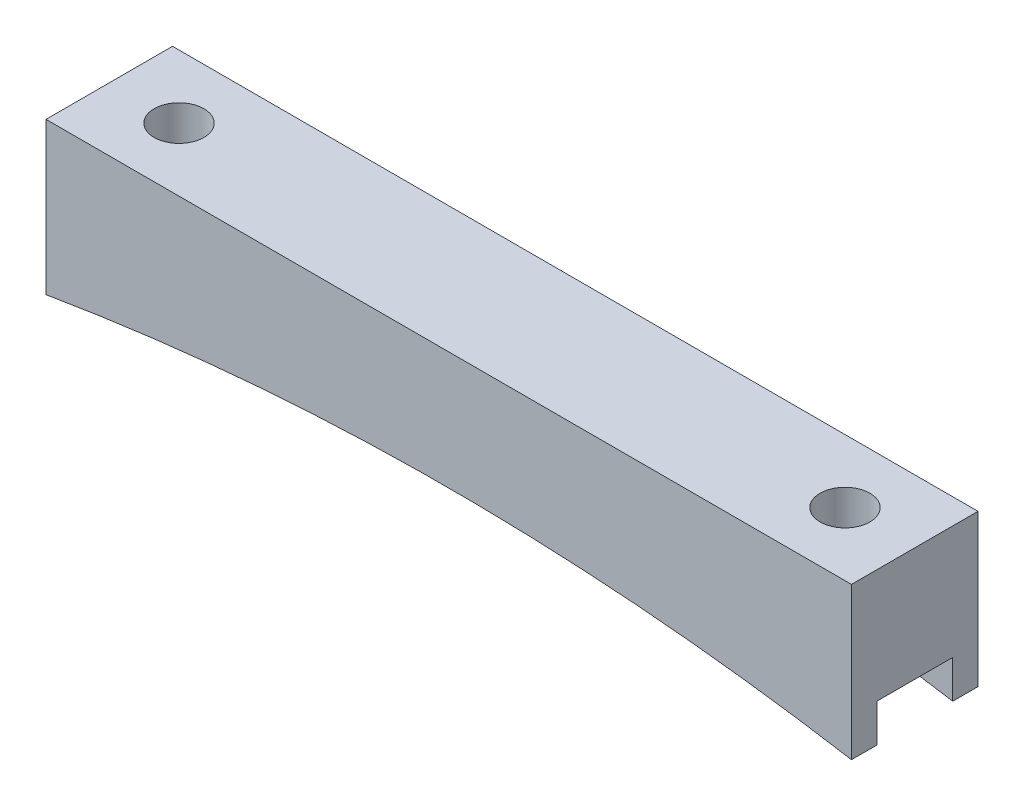
SolidWorks part; units mm, degrees
ref_plane "Front Plane" through (0, 0, 0) normal (0, 0, 1) x (1, 0, 0)
ref_plane "Top Plane" through (0, 0, 0) normal (0, 1, 0) x (1, 0, 0)
ref_plane "Right Plane" through (0, 0, 0) normal (1, 0, 0) x (0, 0, -1)
sketch "Sketch1" plane through (0, 0, 0) normal (0, 0, 1) x (1, 0, 0)
  line L0 (-40.4205, 0) -> (40.4205, 0)
  line L1 (-33.4205, -2.54) -> (33.4205, -2.54) construction
  line L2 (0, 0) -> (0, -4.6068) construction
  line L3 (40.4205, 0) -> (40.4205, -15.24)
  line L4 (-40.4205, 0) -> (-40.4205, -15.24)
  arc A0 (-40.4205, -15.24) -> (40.4205, -15.24) centre (0, -253.1305) cw
  point P4 (0, 0)
  point P9 (0, -2.54)
  dimension "D4" = 241.3
  dimension "D1" = 66.8409
  dimension "D2" = 2.54
  dimension "D3" = 7
  dimension "D5" = 15.24
extrude "Boss-Extrude1" add sketch "Sketch1" along normal blind 12.7
sketch "Sketch2" plane through (0, 0, 0) normal (0, 1, 0) x (1, 0, 0)
  line L1 (-33.4205, 0) -> (-33.4205, -12.7) construction
  line L2 (-40.4205, 0) -> (40.4205, 0) construction
  line L3 (40.4205, -12.7) -> (-40.4205, -12.7) construction
  line L4 (33.4205, 0) -> (33.4205, -12.7) construction
  circle A0 centre (-33.4205, -6.35) radius 2.5
  circle A1 centre (33.4205, -6.35) radius 2.5
  circle A2 centre (-33.4205, -6.35) radius 3 construction
  point P7 (-33.4205, -6.35)
  dimension "D1" = 5
  dimension "D2" = 6
extrude "Cut-Extrude1" cut sketch "Sketch2" against normal through all
sketch "Sketch3" plane through (40.4205, 0, 0) normal (1, 0, 0) x (0, 0, -1)
  line L0 (-12.7, -15.24) -> (0, -15.24) construction
  line L1 (-10.16, -15.24) -> (-2.54, -15.24)
  line L2 (-10.16, -15.24) -> (-10.16, -11.43)
  line L3 (-10.16, -11.43) -> (-2.54, -11.43)
  line L4 (-2.54, -15.24) -> (-2.54, -11.43)
  line L5 (-12.7, -15.24) -> (-12.7, 0) construction
  line L6 (0, -15.24) -> (0, 0) construction
  dimension "D1" = 2.54
  dimension "D2" = 2.54
  dimension "D3" = 3.81
extrude "Cut-Extrude2" cut sketch "Sketch3" against normal through all
